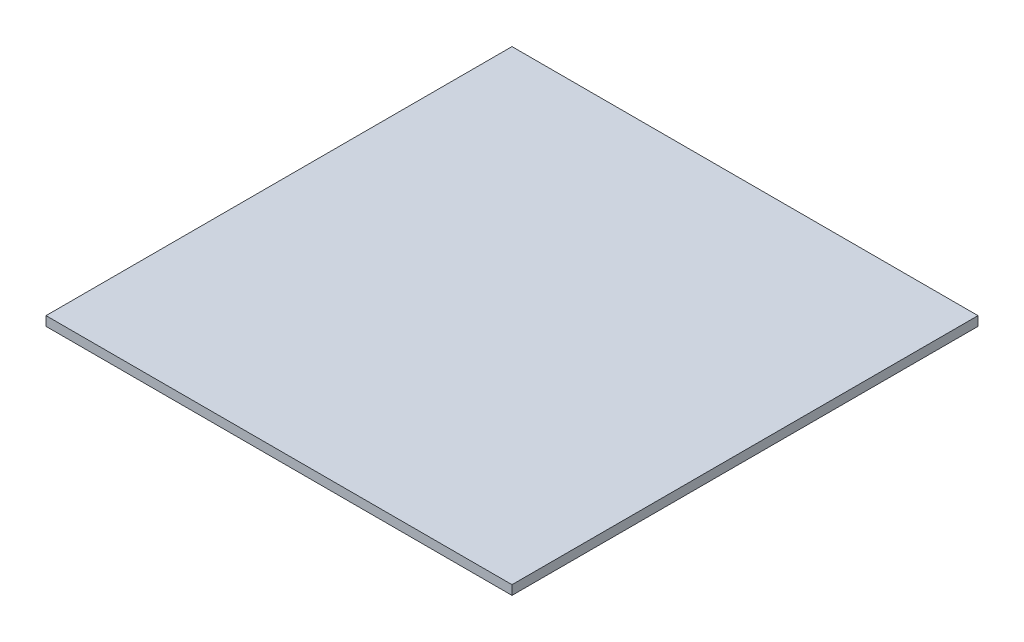
SolidWorks part; units mm, degrees
ref_plane "前视基准面" through (0, 0, 0) normal (0, 0, 1) x (1, 0, 0)
ref_plane "上视基准面" through (0, 0, 0) normal (0, 1, 0) x (1, 0, 0)
ref_plane "右视基准面" through (0, 0, 0) normal (1, 0, 0) x (0, 0, -1)
sketch "草图1" plane through (0, 0, 0) normal (0, 1, 0) x (1, 0, 0)
  line L1 (-500, 500) -> (500, 500)
  line L2 (-500, 500) -> (-500, -500)
  line L3 (-500, -500) -> (500, -500)
  line L4 (500, 500) -> (500, -500)
  line L5 (-500, 500) -> (500, -500) construction
  line L6 (-500, -500) -> (500, 500) construction
  point P0 (0, 0)
  dimension "D1" = 1000
  dimension "D2" = 1000
extrude "凸台-拉伸1" add sketch "草图1" along normal blind 20
sketch "草图2" plane through (0, 20, 0) normal (0, 1, 0) x (1, 0, 0)
  circle A0 centre (0, 0) radius 200
  dimension "D1" = 400
